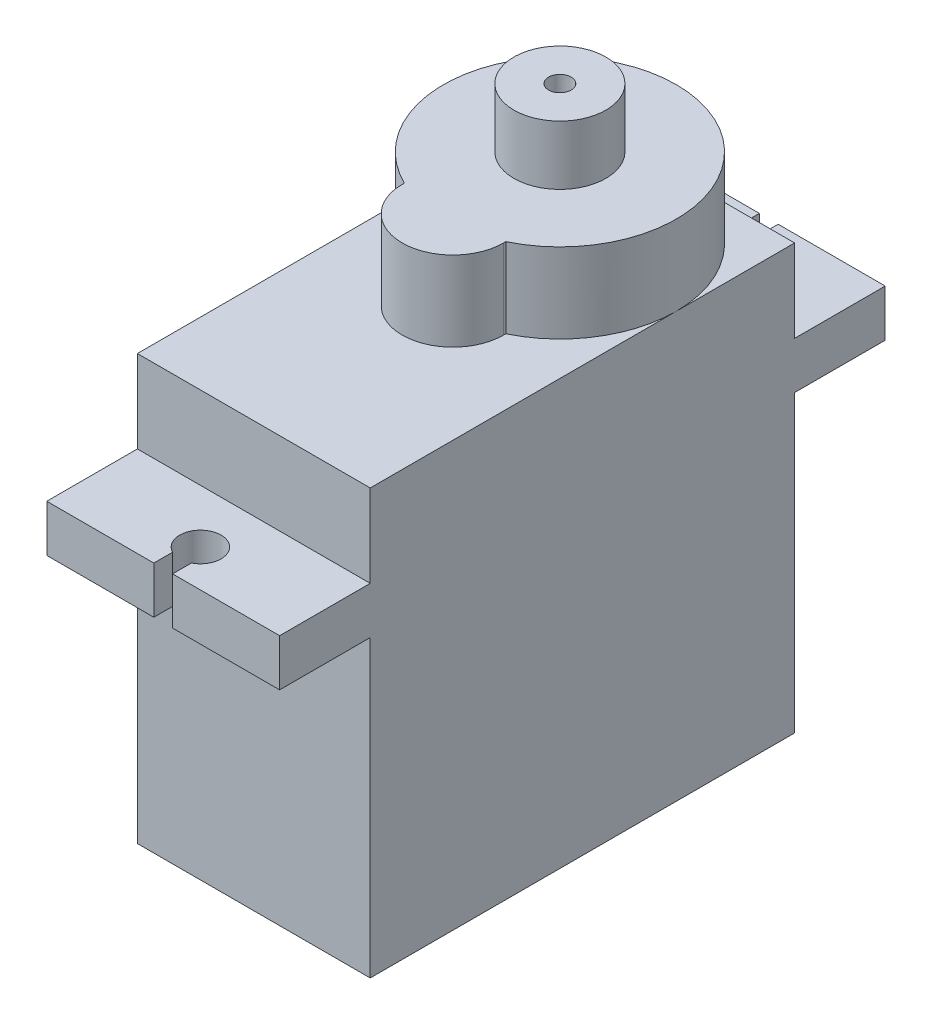
SolidWorks part; units mm, degrees
ref_plane "Ön Düzlem" through (0, 0, 0) normal (0, 0, 1) x (1, 0, 0)
ref_plane "Üst Düzlem" through (0, 0, 0) normal (0, 1, 0) x (1, 0, 0)
ref_plane "Sağ Düzlem" through (0, 0, 0) normal (1, 0, 0) x (0, 0, -1)
sketch "Çizim1" plane through (0, 0, 0) normal (0, 1, 0) x (1, 0, 0)
  line L1 (-6.2, -11.3) -> (6.2, -11.3)
  line L2 (-6.2, -11.3) -> (-6.2, 11.3)
  line L3 (-6.2, 11.3) -> (6.2, 11.3)
  line L4 (6.2, -11.3) -> (6.2, 11.3)
  line L5 (-6.2, -11.3) -> (6.2, 11.3) construction
  line L6 (-6.2, 11.3) -> (6.2, -11.3) construction
  point P0 (0, 0)
  dimension "D1" = 12.4
  dimension "D2" = 22.6
extrude "Yükseklik-Ekstrüzyon1" add sketch "Çizim1" along normal blind 22.6
ref_plane "Düzlem1" through (0, 18.2, 0) normal (0, 1, 0) x (1, 0, 0)
sketch "Çizim2" plane through (0, 18.2, 0) normal (0, 1, 0) x (1, 0, 0)
  line L0 (6.2, -11.3) -> (6.2, 11.3) construction
  line L1 (-6.2, -16.125) -> (6.2, -16.125)
  line L2 (-6.2, -16.125) -> (-6.2, 16.125)
  line L3 (-6.2, 16.125) -> (6.2, 16.125)
  line L4 (6.2, -16.125) -> (6.2, 16.125)
  line L5 (-6.2, -16.125) -> (6.2, 16.125) construction
  line L6 (-6.2, 16.125) -> (6.2, -16.125) construction
  line L7 (0, 14.1452) -> (0, 16.125) construction
  line L8 (0.5, 15.125) -> (0.5, 16.125)
  line L9 (-0.5, 15.125) -> (-0.5, 16.125)
  line L10 (-0.5, 16.125) -> (0.5, 16.125)
  line L11 (-6.2, 0) -> (6.2, 0) construction
  line L12 (0.5, -15.125) -> (0.5, -16.125)
  line L13 (-0.5, -15.125) -> (-0.5, -16.125)
  circle A0 centre (0, 14.1452) radius 1.1
  circle A1 centre (0, -14.1452) radius 1.1
  point P0 (0, 0)
  dimension "D2" = 2.2
  dimension "D1" = 32.25
  dimension "D3" = 1
  dimension "D4" = 0.5
extrude "Yükseklik-Ekstrüzyon2" add sketch "Çizim2" against normal blind 2.5 contours L13 A1 L12 L1 L4 L3 L8 A0 L9 L2
ref_plane "Düzlem2" through (0, 4.8, 0) normal (0, -1, 0) x (-1, 0, 0)
sketch "Çizim3" plane through (0, 4.8, 0) normal (0, -1, 0) x (-1, 0, 0)
  line L0 (-1.8, 11.3) -> (1.8, 11.3)
  line L1 (-1.8, 11.3) -> (-1.8, 14.3)
  line L2 (1.8, 11.3) -> (1.8, 14.3)
  line L3 (-1.8, 14.3) -> (1.8, 14.3)
  line L4 (-6.2, 11.3) -> (6.2, 11.3) construction
  line L5 (-6.2, 11.3) -> (6.2, 11.3) construction
  point P8 (0, 11.3)
  dimension "D1" = 3.6
  dimension "D2" = 3
extrude "Yükseklik-Ekstrüzyon3" add sketch "Çizim3" along normal blind 1.2
sketch "Çizim4" plane through (0, 22.6, 0) normal (0, 1, 0) x (1, 0, 0)
  line L0 (-6.2, 11.3) -> (-6.2, -11.3) construction
  line L2 (6.2, -11.3) -> (6.2, 11.3) construction
  line L3 (6.2, 11.3) -> (-6.2, 11.3) construction
  line L4 (-2.7, -0.7) -> (-2.7, -0.5812)
  line L5 (2.7, -0.7) -> (2.7, -0.5812)
  circle A0 centre (0, 5) radius 6.2
  arc A1 (-2.7, -0.7) -> (2.7, -0.7) centre (0, -0.7) ccw
  point P2 (0, 11.2)
  point P8 (0, 11.3)
  point P15 (0, -3.4)
  dimension "D2" = 2.7
  dimension "D1" = 0.1
  dimension "D3" = 14.6
extrude "Yükseklik-Ekstrüzyon4" add sketch "Çizim4" along normal blind 4.25 contours A0 | L4 A1 L5 A0
sketch "Çizim5" plane through (0, 26.85, 0) normal (0, 1, 0) x (1, 0, 0)
  circle A0 centre (0, 5) radius 0.6
  arc A1 (6.2, 5) -> (-6.2, 5) centre (0, 5) ccw construction
  circle A2 centre (0, 5) radius 2.45
  arc A3 (2.7, -0.5812) -> (-2.7, -0.5812) centre (0, 5) ccw construction
  dimension "D1" = 1.2
  dimension "D2" = 4.9
ref_plane "Düzlem3" through (0, 30, 0) normal (0, 1, 0) x (1, 0, 0)
extrude "Yükseklik-Ekstrüzyon6" add sketch "Çizim5" along normal up to surface (3.15 mm away) up to plane "Düzlem3"
sketch "Çizim6" plane through (0, 0, -14.3) normal (0, 0, -1) x (-1, 0, 0)
  line L0 (-1.8, 3.6) -> (1.8, 3.6) construction
  line L1 (-0.6667, 3.6) -> (-0.5667, 3.6)
  line L2 (-0.6667, 3.6) -> (-0.6667, 4.8)
  line L3 (-0.6667, 4.8) -> (-0.5667, 4.8)
  line L4 (-0.5667, 3.6) -> (-0.5667, 4.8)
  line L5 (1.8, 4.8) -> (-1.8, 4.8) construction
  line L6 (-0.6667, 4.2) -> (-1.8, 4.2) construction
  line L7 (0.5667, 4.8) -> (0.6667, 4.8)
  line L8 (0.5667, 4.8) -> (0.5667, 3.6)
  line L9 (0.5667, 3.6) -> (0.6667, 3.6)
  line L10 (0.6667, 4.8) -> (0.6667, 3.6)
  line L11 (-1.8, 3.6) -> (-1.8, 4.8) construction
  line L12 (-0.5667, 4.2) -> (0.5667, 4.2) construction
  line L13 (0.6667, 4.2) -> (1.8, 4.2) construction
  line L14 (1.8, 3.6) -> (1.8, 4.8) construction
  dimension "D1" = 0.1
  dimension "D2" = 0.1
extrude "Kes-Ekstrüzyon1" cut sketch "Çizim6" against normal up to surface (3 mm away) up to face at (0, 7.85, -11.3)
fillet "Radyus1" radius 0.5 12 edges at (-0.6667, 4.8, -12.8) (-1.8, 4.8, -12.8) (-1.8, 3.6, -12.8) (-0.6667, 3.6, -12.8) (0.5667, 3.6, -12.8) (-0.5667, 3.6, -12.8) (-0.5667, 4.8, -12.8) (0.5667, 4.8, -12.8) (1.8, 3.6, -12.8) (0.6667, 4.8, -12.8) (0.6667, 3.6, -12.8) (1.8, 4.8, -12.8)
